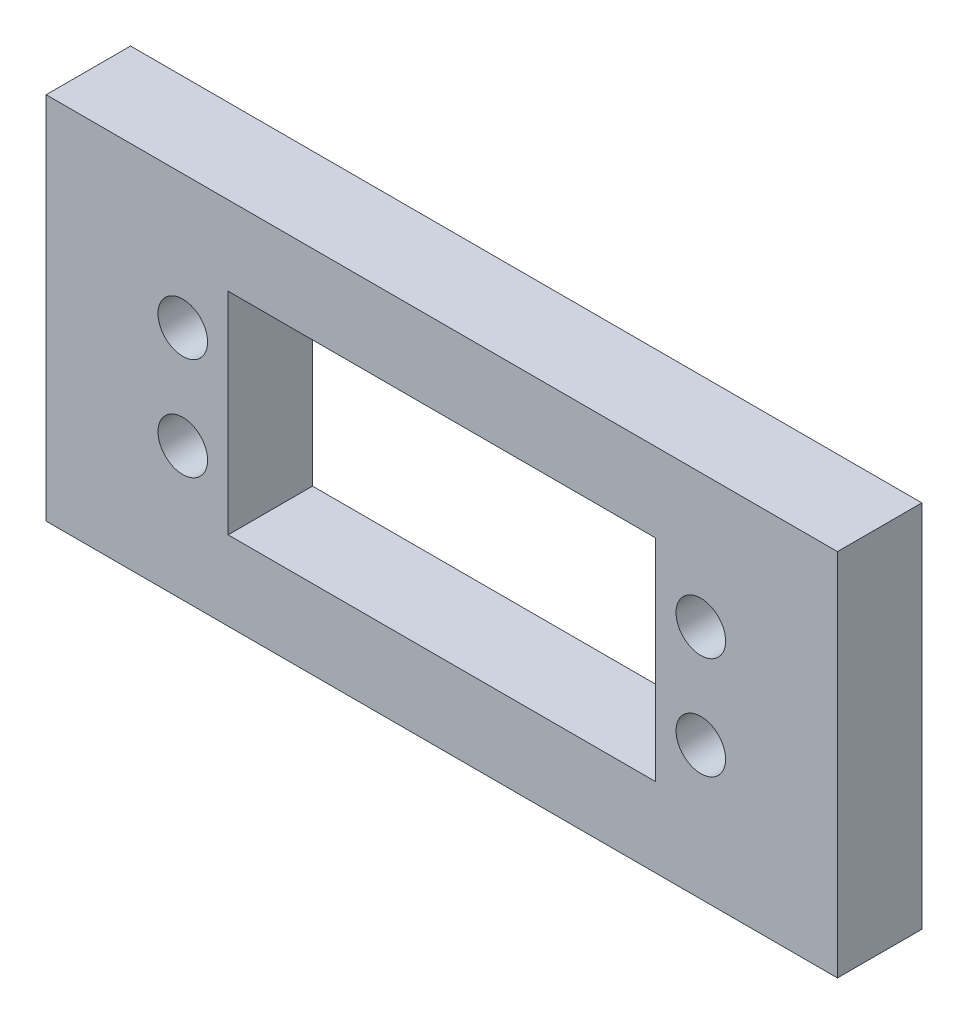
SolidWorks part; units mm, degrees
ref_plane "Front Plane" through (0, 0, 0) normal (0, 0, 1) x (1, 0, 0)
ref_plane "Top Plane" through (0, 0, 0) normal (0, 1, 0) x (1, 0, 0)
ref_plane "Right Plane" through (0, 0, 0) normal (1, 0, 0) x (0, 0, -1)
sketch "Sketch2" plane through (0, 0, 0) normal (0, 0, 1) x (1, 0, 0)
  line L1 (52, -33) -> (-52, -33)
  line L2 (52, -33) -> (52, 33)
  line L3 (52, 33) -> (-52, 33)
  line L4 (-52, -33) -> (-52, 33)
  line L5 (52, -33) -> (-52, 33) construction
  line L6 (52, 33) -> (-52, -33) construction
  point P0 (0, 0)
  dimension "D1" = 104
  dimension "D2" = 66
extrude "Boss-Extrude1" add sketch "Sketch2" along normal blind 8
sketch "Sketch3" plane through (0, 0, 8) normal (0, 0, 1) x (1, 0, 0)
  line L0 (-52, -17) -> (-60, -17)
  line L1 (-52, 33) -> (-52, -33) construction
  line L2 (-60, -17) -> (-60, -22)
  line L3 (-60, -22) -> (-64, -22)
  line L4 (-64, -22) -> (-64, -2)
  line L5 (-64, -2) -> (-60, -2)
  line L6 (-60, -2) -> (-60, -7)
  line L7 (-60, -7) -> (-52, -7)
  line L8 (-52, -7) -> (-52, -17) construction
  line L9 (-52, -7) -> (-52, -17)
  line L10 (-52, -33) -> (52, -33) construction
  line L11 (-52, 13) -> (-60, 13)
  line L12 (-52, 23) -> (-52, 13)
  line L13 (-60, 23) -> (-52, 23)
  line L14 (-60, 28) -> (-60, 23)
  line L15 (-64, 28) -> (-60, 28)
  line L16 (-64, 8) -> (-64, 28)
  line L17 (-60, 8) -> (-64, 8)
  line L18 (-60, 13) -> (-60, 8)
  line L19 (0, 0) -> (0, -19.6599) construction
  line L20 (52, -7) -> (52, -17) construction
  line L21 (52, -7) -> (52, -17)
  line L22 (60, -7) -> (52, -7)
  line L23 (60, -2) -> (60, -7)
  line L24 (64, -2) -> (60, -2)
  line L25 (64, -22) -> (64, -2)
  line L26 (60, -22) -> (64, -22)
  line L27 (60, -17) -> (60, -22)
  line L28 (52, -17) -> (60, -17)
  line L29 (-32.5, -33) -> (-32.5, -41)
  line L30 (-32.5, -41) -> (-37.5, -41)
  line L31 (-37.5, -41) -> (-37.5, -76)
  line L34 (17.5, -41) -> (-17.5, -41)
  line L35 (-17.5, -41) -> (-17.5, -33)
  line L36 (-17.5, -33) -> (-32.5, -33)
  line L45 (-17.5, -33) -> (17.5, -33) construction
  line L46 (-37.5, -76) -> (37.5, -76)
  line L47 (17.5, -33) -> (32.5, -33)
  line L48 (17.5, -41) -> (17.5, -33)
  line L49 (37.5, -41) -> (37.5, -76)
  line L50 (32.5, -41) -> (37.5, -41)
  line L51 (32.5, -33) -> (32.5, -41)
  point P4 (-64, -12)
  point P11 (-52, -12)
  point P44 (0, -33)
  point P46 (0, -76)
  point P48 (0, -41)
  dimension "D1" = 10
  dimension "D2" = 2
  dimension "D3" = 8
  dimension "D4" = 16
  dimension "D5" = 20
  dimension "D6" = 4
  dimension "D7" = 20
  dimension "D8" = 15
  dimension "D9" = 5
  dimension "D10" = 8
  dimension "D11" = 35
  dimension "D12" = 17.5
extrude "Boss-Extrude2" add sketch "Sketch3" against normal through all
sketch "Sketch4" plane through (0, 0, 8) normal (0, 0, 1) x (1, 0, 0)
  line L0 (52, -7) -> (52, 33) construction
  line L1 (-52, 33) -> (52, 33)
  line L2 (-52, 33) -> (-52, 23)
  line L3 (-52, 23) -> (52, 23)
  line L4 (52, 33) -> (52, 23)
  dimension "D1" = 10
extrude "Cut-Extrude1" cut sketch "Sketch4" against normal blind 8
sketch "Sketch6" plane through (0, 0, 8) normal (0, 0, 1) x (1, 0, 0)
  line L0 (-60, 23) -> (52, 23) construction
  line L1 (52, -7) -> (52, 23) construction
  line L2 (52, 17) -> (52, 0)
  line L3 (52, 0) -> (0, 0)
  line L4 (0, 0) -> (0, 23)
  line L5 (0, 23) -> (42, 23)
  line L6 (52, -7) -> (52, 23) construction
  line L7 (52, 23) -> (-60, 23) construction
  arc A0 (42, 23) -> (52, 17) centre (51.7989, 27.9982) cw
  dimension "D1" = 10
  dimension "D2" = 6
extrude "Boss-Extrude4" add sketch "Sketch6" against normal blind 8
sketch "Sketch8" plane through (0, 0, 8) normal (0, 0, 1) x (1, 0, 0)
  line L1 (47.2877, 17.9658) -> (41.2877, 7.5735)
  line L2 (52, 17) -> (52, 5.0283)
  line L3 (52, -7) -> (52, 17) construction
  arc A3 (41.2877, 7.5735) -> (52, 5.0283) centre (51.7989, 27.9982) ccw
  arc A4 (47.2877, 17.9658) -> (52, 17) centre (51.7989, 27.9982) ccw
  arc A5 (52, 17) -> (42, 23) centre (51.7989, 27.9982) ccw construction
  dimension "D2" = 30
  dimension "D1" = 12
extrude "Cut-Extrude2" cut sketch "Sketch8" against normal blind 8
sketch "Sketch9" plane through (0, 0, 8) normal (0, 0, 1) x (1, 0, 0)
  line L5 (53.8565, 29.4182) -> (49.7413, 26.5782) construction
  arc A0 (47.2877, 17.9658) -> (42, 23) centre (51.7989, 27.9982) ccw construction
  circle A1 centre (51.7989, 27.9982) radius 2.5
  point P0 (51.7989, 27.9982)
  dimension "D1" = 5
extrude "Cut-Extrude3" cut sketch "Sketch9" against normal through all
sketch "Sketch10" plane through (0, 0, 8) normal (0, 0, 1) x (1, 0, 0)
  line L0 (-24.55, -58.5) -> (-37.5, -58.5) construction
  line L9 (-24.55, -53.65) -> (24.55, -53.65) construction
  line L10 (-24.55, -53.65) -> (-24.55, -63.35) construction
  line L11 (-24.55, -63.35) -> (24.55, -63.35) construction
  line L13 (24.55, -53.65) -> (24.55, -63.35) construction
  line L14 (-24.55, -53.65) -> (24.55, -63.35) construction
  line L15 (-24.55, -63.35) -> (24.55, -53.65) construction
  line L16 (0, -53.65) -> (0, -46.0939) construction
  line L17 (-20.25, -48.5) -> (20.25, -48.5)
  line L18 (-20.25, -48.5) -> (-20.25, -68.5)
  line L19 (-20.25, -68.5) -> (20.25, -68.5)
  line L20 (-37.5, -41) -> (37.5, -41) construction
  line L21 (-37.5, -41) -> (-37.5, -76) construction
  line L22 (20.25, -48.5) -> (20.25, -68.5)
  line L23 (-20.25, -48.5) -> (20.25, -68.5) construction
  line L24 (-20.25, -68.5) -> (20.25, -48.5) construction
  line L25 (0, -46.0939) -> (0, -41) construction
  line L26 (17.5, -41) -> (-17.5, -41) construction
  line L27 (-37.5, -41) -> (-37.5, -76) construction
  line L28 (-37.5, -76) -> (37.5, -76) construction
  line L29 (37.5, -41) -> (37.5, -76) construction
  line L30 (-37.5, -41) -> (37.5, -76) construction
  line L31 (-37.5, -76) -> (37.5, -41) construction
  circle A8 centre (-24.55, -53.65) radius 2.35
  circle A9 centre (-24.55, -63.35) radius 2.35
  circle A10 centre (24.55, -63.35) radius 2.35
  circle A11 centre (24.55, -53.65) radius 2.35
  point P0 (-24.55, -53.65)
  point P1 (-24.55, -63.35)
  point P3 (24.55, -63.35)
  point P5 (24.55, -53.65)
  point P11 (0, -58.5)
  point P23 (0, -58.5)
  point P31 (0, -58.5)
  dimension "D3" = 4.7
  dimension "D1" = 49.1
  dimension "D2" = 9.7
  dimension "D4" = 40.5
  dimension "D5" = 20
extrude "Cut-Extrude4" cut sketch "Sketch10" against normal up to next
sketch "Sketch11" plane through (0, 0, 8) normal (0, 0, 1) x (1, 0, 0)
  line L1 (64, -41) -> (-64, -41)
  line L2 (64, -41) -> (64, 41)
  line L3 (64, 41) -> (-64, 41)
  line L4 (-64, -41) -> (-64, 41)
  line L5 (64, -41) -> (-64, 41) construction
  line L6 (64, 41) -> (-64, -41) construction
  point P4 (0, 0)
extrude "Cut-Extrude5" cut sketch "Sketch11" against normal up to next
equation "\"e\" = 5.9"
